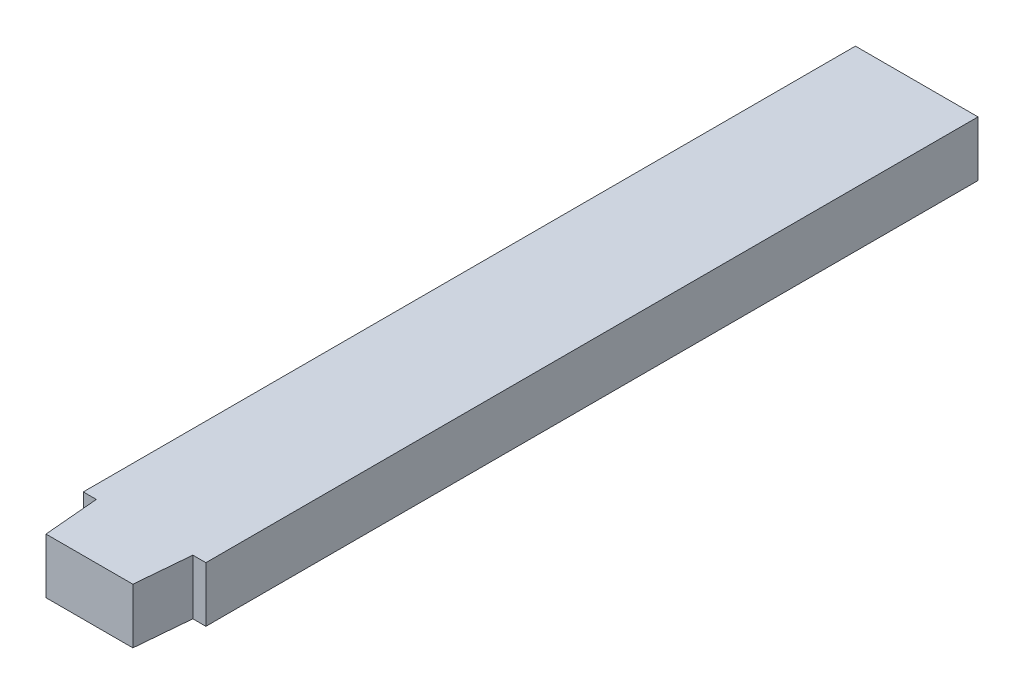
SolidWorks part; units mm, degrees
ref_plane "Front Plane" through (0, 0, 0) normal (0, 0, 1) x (1, 0, 0)
ref_plane "Top Plane" through (0, 0, 0) normal (0, 1, 0) x (1, 0, 0)
ref_plane "Right Plane" through (0, 0, 0) normal (1, 0, 0) x (0, 0, -1)
sketch "Sketch1" plane through (0, 0, 0) normal (0, 1, 0) x (1, 0, 0)
  line L0 (0, -322.1883) -> (0, 15787.2269) construction
  line L2 (-6.35, 40) -> (6.35, 40)
  line L3 (-6.35, 40) -> (-6.35, -40)
  line L4 (-6.35, -40) -> (6.35, -40)
  line L5 (6.35, 40) -> (6.35, -40)
  line L6 (-6.35, 40) -> (6.35, -40) construction
  line L7 (-6.35, -40) -> (6.35, 40) construction
  line L8 (-5, -40) -> (5, -40)
  line L9 (-5, -40) -> (-4.5, -45.715)
  line L10 (-4.5, -45.715) -> (4.5, -45.715)
  line L11 (5, -40) -> (4.5, -45.715)
  point P1 (0, 0)
  point P8 (0, -40)
  point P14 (0, -45.715)
  dimension "D2" = 80
  dimension "D3" = 10
  dimension "D4" = 9
  dimension "D5" = 5.715
extrude "Boss-Extrude1" add sketch "Sketch1" along normal blind 5.715 contours L5 L2 L3 L4 | L11 L4 L9 L10
equation "\"magnetWidth\" = 0.0127"
equation "\"quarterInch\" = 0.005715"
equation "\"coilThickness\" = 0.0254"
equation "\"coilOuterDiameter\" = 0.0508"
equation "\"legoThickness\" = 0.008"
equation "\"legoWidth\" = 0.016"
equation "\"toothBaseWidth\"=0.01"
equation "\"toothEndWidth\"=0.009"
equation "\"toothLength\"= 0.005715"
equation "\"holeWidth\" = 0.009"
equation "\"motorHolderToothSeparation\" = 0.01"
equation "\"magnetHolderToothSeparation\" = 0.02"
equation "\"D3@Sketch1\"=\"toothBaseWidth\""
equation "\"D4@Sketch1\"=\"toothEndWidth\""
equation "\"D5@Sketch1\"=\"toothLength\""
equation "\"D1@Boss-Extrude1\"=\"quarterInch\""
